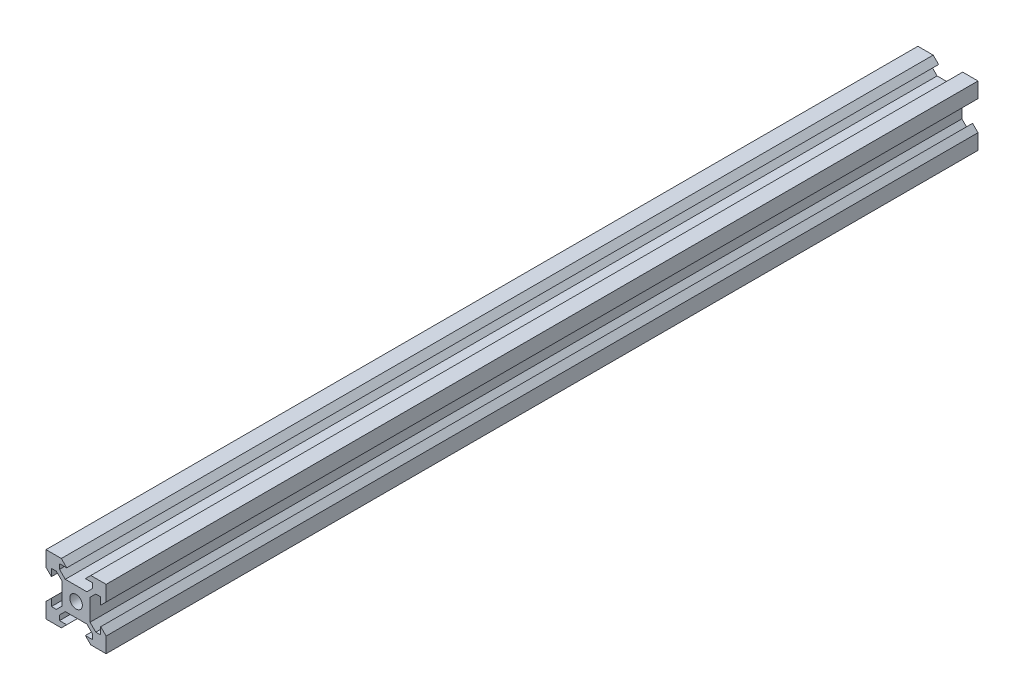
SolidWorks part; units mm, degrees
material "6063-T5"
ref_plane "Front Plane" through (0, 0, 0) normal (0, 0, 1) x (1, 0, 0)
ref_plane "Top Plane" through (0, 0, 0) normal (0, 1, 0) x (1, 0, 0)
ref_plane "Right Plane" through (0, 0, 0) normal (1, 0, 0) x (0, 0, -1)
sketch "Sketch1" plane through (0, 0, 0) normal (0, 0, 1) x (1, 0, 0)
  line L0 (3.59, 4.6507) -> (-3.59, 4.6507)
  line L5 (-10, -10) -> (10, -10)
  line L6 (-10, -10) -> (-10, 10)
  line L7 (-10, 10) -> (10, 10)
  line L8 (10, -10) -> (10, 10)
  line L9 (-10, -10) -> (10, 10) construction
  line L10 (-10, 10) -> (10, -10) construction
  line L11 (0, 10) -> (0, -10) construction
  line L12 (10, 0) -> (-10, 0) construction
  line L13 (-3.59, 4.6507) -> (-5.4993, 6.56)
  line L14 (-5.4993, 6.56) -> (-5.4993, 8.2)
  line L15 (3.59, 4.6507) -> (5.4993, 6.56)
  line L16 (5.4993, 6.56) -> (5.4993, 8.2)
  line L17 (5.4993, 8.2) -> (3.1, 8.2)
  line L18 (3.1, 8.2) -> (4.9, 10)
  line L19 (-5.4993, 8.2) -> (-3.1, 8.2)
  line L20 (-3.1, 8.2) -> (-4.9, 10)
  line L21 (3.1, -8.2) -> (4.9, -10)
  line L22 (5.4993, -8.2) -> (3.1, -8.2)
  line L23 (5.4993, -6.56) -> (5.4993, -8.2)
  line L24 (3.59, -4.6507) -> (5.4993, -6.56)
  line L25 (3.59, -4.6507) -> (-3.59, -4.6507)
  line L26 (-3.59, -4.6507) -> (-5.4993, -6.56)
  line L27 (-5.4993, -6.56) -> (-5.4993, -8.2)
  line L28 (-5.4993, -8.2) -> (-3.1, -8.2)
  line L29 (-3.1, -8.2) -> (-4.9, -10)
  line L30 (8.2, 3.1) -> (10, 4.9)
  line L31 (8.2, 3.1) -> (8.2, 5.4993)
  line L32 (8.2, 5.4993) -> (6.56, 5.4993)
  line L33 (4.6507, 3.59) -> (6.56, 5.4993)
  line L34 (4.6507, 3.59) -> (4.6507, -3.59)
  line L35 (4.6507, -3.59) -> (6.56, -5.4993)
  line L36 (8.2, -5.4993) -> (6.56, -5.4993)
  line L37 (8.2, -3.1) -> (8.2, -5.4993)
  line L38 (8.2, -3.1) -> (10, -4.9)
  line L39 (-8.2, -3.1) -> (-10, -4.9)
  line L40 (-8.2, -3.1) -> (-8.2, -5.4993)
  line L41 (-8.2, -5.4993) -> (-6.56, -5.4993)
  line L42 (-4.6507, -3.59) -> (-6.56, -5.4993)
  line L43 (-4.6507, 3.59) -> (-4.6507, -3.59)
  line L44 (-4.6507, 3.59) -> (-6.56, 5.4993)
  line L45 (-8.2, 5.4993) -> (-6.56, 5.4993)
  line L46 (-8.2, 3.1) -> (-8.2, 5.4993)
  line L47 (-8.2, 3.1) -> (-10, 4.9)
  line L48 (4.9, 10) -> (-4.9, 10)
  line L49 (-10, 4.9) -> (-10, -4.9)
  line L50 (10, -4.9) -> (10, 4.9)
  line L51 (4.9, -10) -> (-4.9, -10)
  circle A1 centre (0, 0) radius 2.1
  point P11 (0, 4.6507)
  point P35 (4.6507, 0)
  dimension "D1" = 4.2
  dimension "D2" = 20
  dimension "D3" = 20
  dimension "D4" = 0.75
  dimension "D5" = 3.59
  dimension "D6" = 3.1
  dimension "D7" = 1.8
  dimension "D8" = 1.64
  dimension "D9" = 3.59
  dimension "D10" = 1.64
  dimension "D11" = 1.8
  dimension "D12" = 45
  dimension "D13" = 0.75
  dimension "D14" = 3.1
extrude "Boss-Extrude1" add sketch "Sketch1" along normal mid plane 290 contours L6 L5 L8 L7 | A1 | L50 L30 L31 L32 L33 L34 L35 L36 L37 L38 | L48 L20 L19 L14 L13 L0 L15 L16 L17 L18 | L49 L39 L40 L41 L42 L43 L44 L45 L46 L47 | L51 L29 L28 L27 L26 L25 L24 L23 L22 L21
